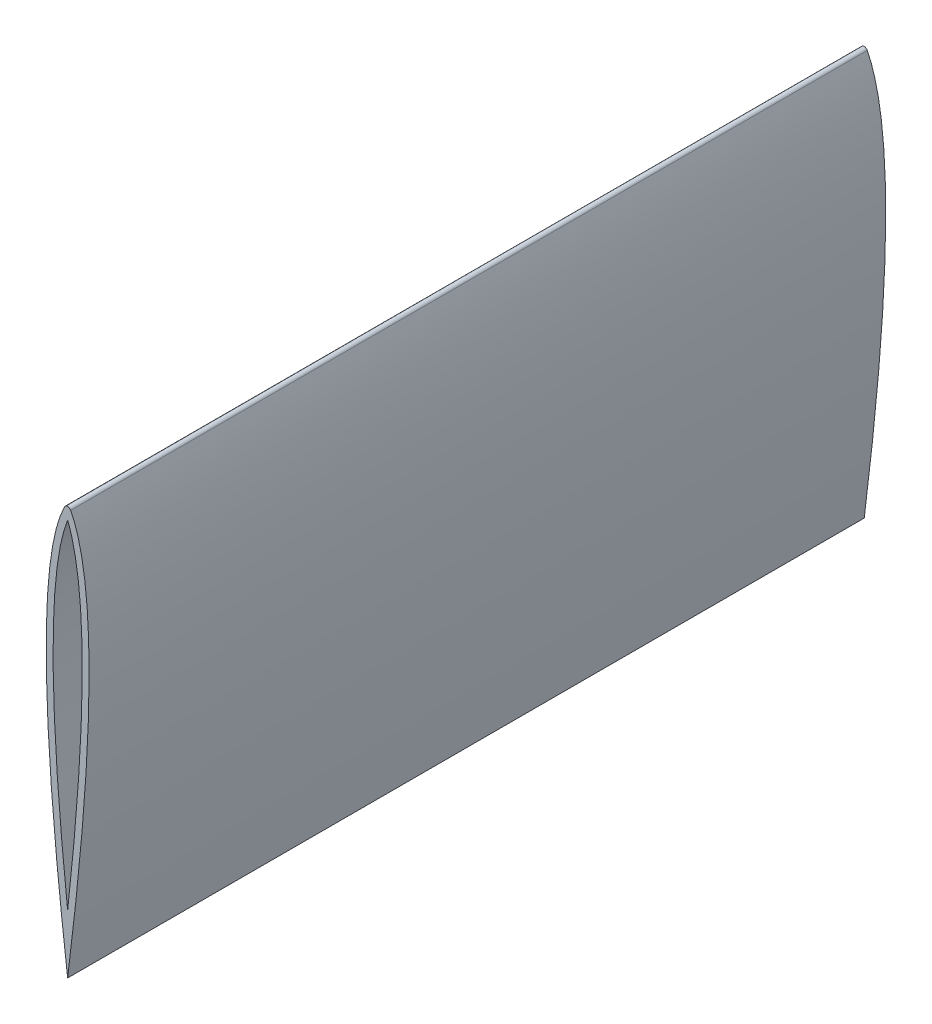
SolidWorks part; units mm, degrees
material "Acrylic (Medium-high impact)"
ref_plane "Front Plane" through (0, 0, 0) normal (0, 0, 1) x (1, 0, 0)
ref_plane "Top Plane" through (0, 0, 0) normal (0, 1, 0) x (1, 0, 0)
ref_plane "Right Plane" through (0, 0, 0) normal (1, 0, 0) x (0, 0, -1)
sketch "Sketch1" plane through (0, 0, 0) normal (0, 0, 1) x (1, 0, 0)
  line L0 (-2.2678, 148.3484) -> (-30.5724, 92.2411) construction
  line L1 (-30.5724, 92.2411) -> (0, -152.4) construction
  line L6 (2.2678, 148.3484) -> (30.5724, 92.2411) construction
  line L7 (30.5724, 92.2411) -> (0, -152.4) construction
  arc A0 (-2.2678, 148.3484) -> (2.2678, 148.3484) centre (0, 147.2043) cw
  arc A1 (0, 140.978) -> (0, 140.978) centre (0, 140.978) cw
  spline S0 degree 2 poles (-2.2678, 148.3484) (-30.5724, 92.2411) (0, -152.4) knots 0 0 0 1 1 1
  spline S1 degree 2 poles (2.2678, 148.3484) (30.5724, 92.2411) (0, -152.4) knots 0 0 0 1 1 1
  spline S2 degree 1 poles (0, 140.978) (0, -109.1253) knots 0 0 1 1 construction
  spline S3 degree 1 poles (0, 140.978) (0, -109.1253) knots 0 0 1 1 construction
  spline S4 degree 2 poles (0, 140.978) (3.9185, 131.1561) (8.1694, 106.0556) (10.2426, 81.4333) (11.1457, 45.0402) (8.1637, -35.5088) (0, -109.1253) knots 0.045527 0.045527 0.045527 0.207531 0.315533 0.423536 0.585539 0.909547 0.909547 0.909547
  spline S5 degree 2 poles (0, -109.1253) (-8.1637, -35.5088) (-11.1457, 45.0402) (-10.2426, 81.4333) (-8.1694, 106.0556) (-3.9185, 131.1561) (0, 140.978) knots 0.045527 0.045527 0.045527 0.369534 0.531538 0.639541 0.747543 0.909547 0.909547 0.909547
  dimension "D1" = 2.54
  dimension "D2" = 5.08
extrude "Boss-Extrude1" add sketch "Sketch1" along normal mid plane 589.28
sketch "Sketch2" plane through (0, 0, 0) normal (0, 0, 1) x (1, 0, 0)
  line L0 (-2.2678, 148.3484) -> (-30.5724, 92.2411) construction
  line L1 (-30.5724, 92.2411) -> (0, -152.4) construction
  line L2 (0, 57.15) -> (0, -6.35) construction
  line L6 (2.2678, 148.3484) -> (30.5724, 92.2411) construction
  line L7 (30.5724, 92.2411) -> (0, -152.4) construction
  line L8 (3.81, 57.15) -> (3.81, -6.35)
  line L9 (-3.81, 57.15) -> (-3.81, -6.35)
  arc A0 (-2.2678, 148.3484) -> (2.2678, 148.3484) centre (0, 147.2043) cw construction
  arc A1 (0, 140.978) -> (0, 140.978) centre (0, 140.978) cw
  circle A2 centre (0, 82.55) radius 3.175
  circle A3 centre (0, -31.75) radius 3.175
  arc A4 (3.81, 57.15) -> (-3.81, 57.15) centre (0, 57.15) ccw
  arc A5 (-3.81, -6.35) -> (3.81, -6.35) centre (0, -6.35) ccw
  spline S0 degree 2 poles (-2.2678, 148.3484) (-30.5724, 92.2411) (0, -152.4) knots 0 0 0 1 1 1 construction
  spline S1 degree 2 poles (2.2678, 148.3484) (30.5724, 92.2411) (0, -152.4) knots 0 0 0 1 1 1 construction
  spline S2 degree 1 poles (0, 140.978) (0, -109.1253) knots 0 0 1 1 construction
  spline S3 degree 1 poles (0, 140.978) (0, -109.1253) knots 0 0 1 1 construction
  spline S4 degree 2 poles (0, 140.978) (3.9185, 131.1561) (8.1694, 106.0556) (10.2426, 81.4333) (11.1457, 45.0402) (8.1637, -35.5088) (0, -109.1253) knots 0.045527 0.045527 0.045527 0.207531 0.315533 0.423536 0.585539 0.909547 0.909547 0.909547
  spline S5 degree 2 poles (0, -109.1253) (-8.1637, -35.5088) (-11.1457, 45.0402) (-10.2426, 81.4333) (-8.1694, 106.0556) (-3.9185, 131.1561) (0, 140.978) knots 0.045527 0.045527 0.045527 0.369534 0.531538 0.639541 0.747543 0.909547 0.909547 0.909547
  point P8 (0, 25.4)
  dimension "D1" = 2.54
  dimension "D3" = 6.35
  dimension "D8" = 3.81
  dimension "D4" = 114.3
  dimension "D5" = 63.5
  dimension "D6" = 57.15
  dimension "D2" = 5.08
